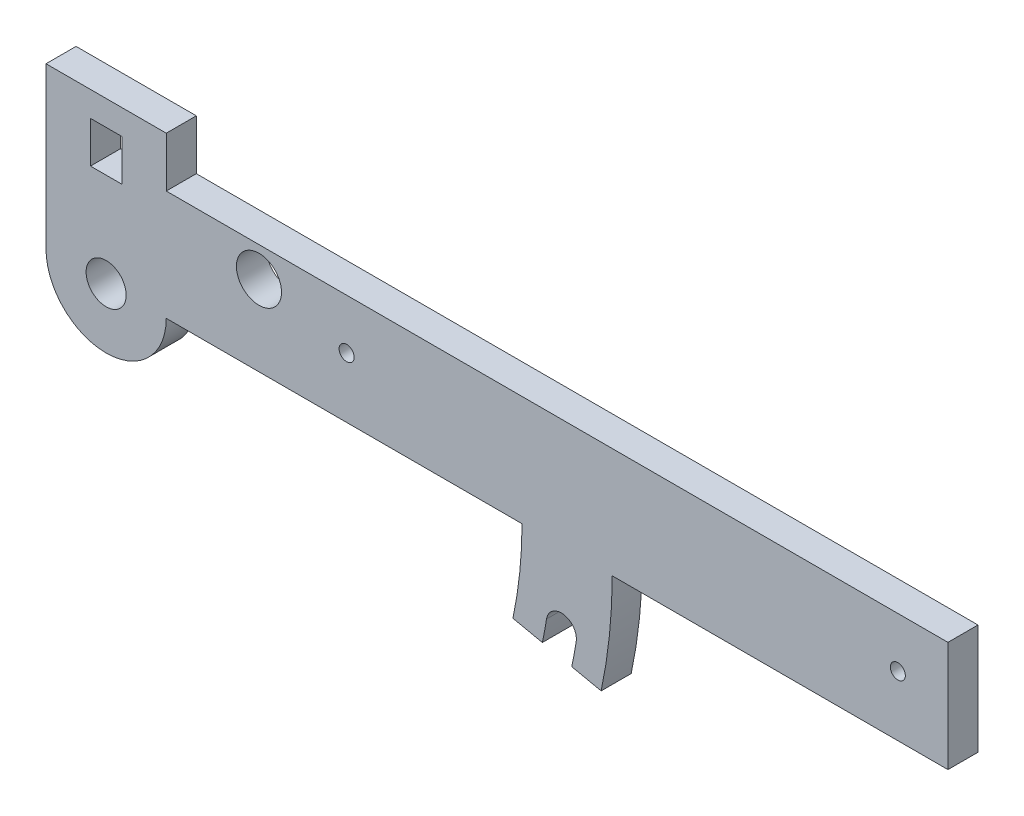
SolidWorks part; units mm, degrees
material "Balsa"
ref_plane "Plano frontal" through (0, 0, 0) normal (0, 0, 1) x (1, 0, 0)
ref_plane "Plano superior" through (0, 0, 0) normal (0, 1, 0) x (1, 0, 0)
ref_plane "Plano direito" through (0, 0, 0) normal (1, 0, 0) x (0, 0, -1)
sketch "Esboço1" plane through (0, 0, 0) normal (0, 0, 1) x (1, 0, 0)
  line L0 (50, -7) -> (50, 15)
  line L1 (-130, 25) -> (-130, -7)
  line L2 (-36.8137, -24.2567) -> (-30.9449, -25.5041)
  line L3 (50, 15) -> (-106, 15)
  line L4 (-25.076, -26.7516) -> (-19.2071, -27.9991)
  line L5 (-106, 15) -> (-106, 25)
  line L6 (-17, -7) -> (50, -7)
  line L7 (-106, 25) -> (-130, 25)
  line L9 (-121.125, 20) -> (-114.875, 20)
  line L10 (-121.125, 20) -> (-121.125, 11.75)
  line L11 (-121.125, 11.75) -> (-114.875, 11.75)
  line L12 (-114.875, 20) -> (-114.875, 11.75)
  line L18 (-106, -7) -> (-35, -7)
  circle A0 centre (-118, -7) radius 4
  arc A1 (-130, -7) -> (-106, -7) centre (-118, -7) ccw
  arc A2 (-26, -7) -> (-28.0104, -26.1279) centre (-118, -7) cw construction
  arc A3 (-30.1124, -21.0272) -> (-30.9449, -25.5041) centre (-118, -7) cw
  arc A4 (-24.1873, -21.9728) -> (-25.076, -26.7516) centre (-118, -7) cw
  arc A5 (-35, -7) -> (-36.8137, -24.2567) centre (-118, -7) cw
  circle A6 centre (-70, 5) radius 1.5
  circle A7 centre (40, 5) radius 1.5
  arc A8 (-17, -7) -> (-19.2071, -27.9991) centre (-118, -7) cw
  arc A9 (-30.1124, -21.0272) -> (-24.1873, -21.9728) centre (-27.1498, -21.5) cw
  arc A10 (-29, -7) -> (-30.9449, -25.5041) centre (-118, -7) cw construction
  arc A11 (-23, -7) -> (-25.076, -26.7516) centre (-118, -7) cw construction
  circle A12 centre (-87.5, 9) radius 4.5
  point P0 (0, 0)
  point P1 (-118, 20)
  point P43 (33.0192, -7)
  point P56 (-1.1739, -7)
  dimension "D13" = 3
  dimension "D15" = 9
  dimension "D5" = 3
  dimension "D3" = 50
  dimension "D4" = 12
  dimension "D10" = 92
  dimension "D17" = 9
  dimension "D18" = 17.5
  dimension "D20" = 110
  dimension "D21" = 10
  dimension "D8" = 8
  dimension "D9" = 24
  dimension "D2" = 10
  dimension "D6" = 10
  dimension "D7" = 12
  dimension "D11" = 3
  dimension "D12" = 5
  dimension "D14" = 9
  dimension "D16" = 14.5
  dimension "D19" = 16
  dimension "D22" = 130
  dimension "D23" = 8.25
  dimension "D24" = 6.25
  dimension "D25" = 5
extrude "Ressalto-extrusão1" add sketch "Esboço1" along normal blind 6
